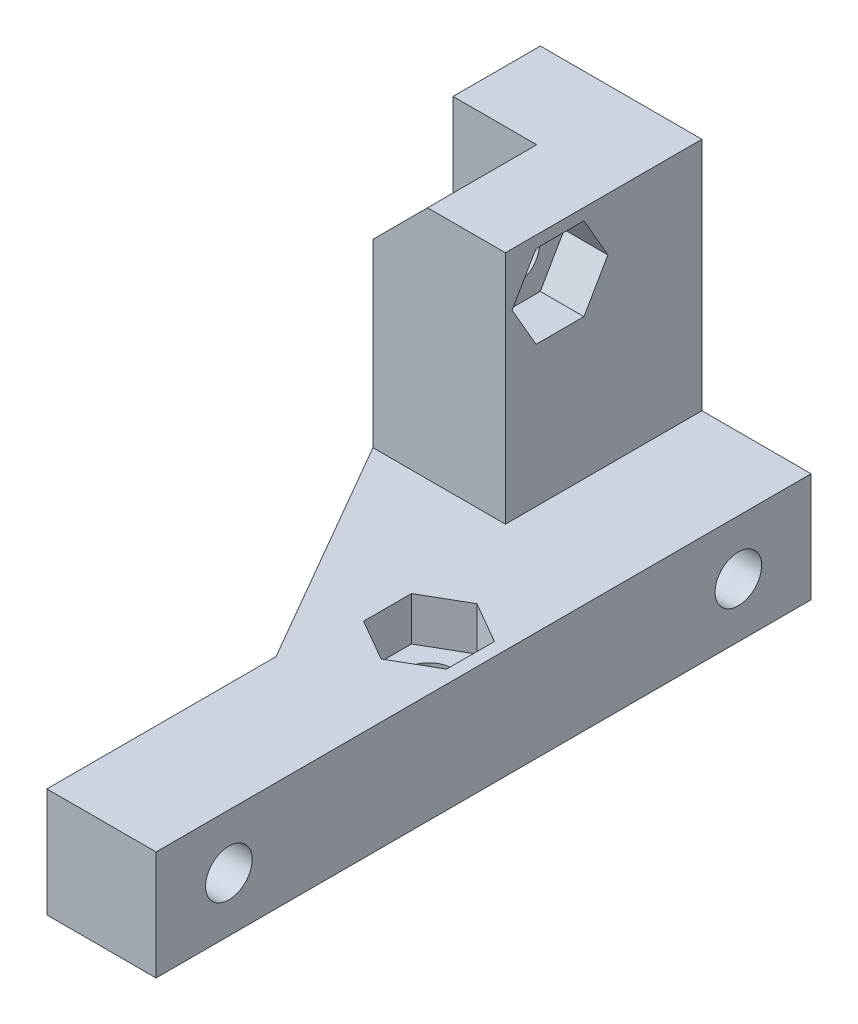
SolidWorks part; units mm, degrees
ref_plane "Alzado" through (0, 0, 0) normal (0, 0, 1) x (1, 0, 0)
ref_plane "Planta" through (0, 0, 0) normal (0, 1, 0) x (1, 0, 0)
ref_plane "Vista lateral" through (0, 0, 0) normal (1, 0, 0) x (0, 0, -1)
sketch "Croquis1" plane through (0, 0, 0) normal (0, 0, 1) x (1, 0, 0)
  line L0 (0, 0) -> (16.6, 0)
  line L1 (16.6, 0) -> (16.6, 7.5)
  line L2 (16.6, 7.5) -> (9.1, 7.5)
  line L3 (9.1, 7.5) -> (9.1, 23.65)
  line L4 (9.1, 23.65) -> (3.75, 23.65)
  line L5 (3.75, 23.65) -> (-2, 23.65)
  line L6 (0, 23.65) -> (0, 0) construction
  line L7 (0, 0) -> (-2, 0)
  line L8 (-2, 0) -> (-2, 23.65)
  line L10 (0, 0) -> (-2, 0)
  dimension "D1" = 7.5
  dimension "D3" = 3.75
  dimension "D4" = 16.6
  dimension "D5" = 7.5
  dimension "D6" = 23.65
  dimension "D7" = 2
extrude "Saliente-Extruir1" add sketch "Croquis1" along normal blind 6 contours L5 L6 L0 L1 L2 L3 L4 | L6 L5 L8 L7
sketch "Croquis2" plane through (0, 0, 6) normal (0, 0, 1) x (1, 0, 0)
  line L0 (0, 0) -> (0, 19.9)
  line L1 (0, 19.9) -> (3.75, 23.65)
  line L6 (9.1, 23.65) -> (-2, 23.65)
  line L7 (-2, 23.65) -> (-2, 0)
  line L8 (-2, 0) -> (16.6, 0)
  line L9 (16.6, 0) -> (16.6, 7.5)
  line L10 (16.6, 7.5) -> (9.1, 7.5)
  line L11 (9.1, 7.5) -> (9.1, 23.65)
  line L12 (9.1, 23.65) -> (3.75, 23.65)
  line L14 (0, 0) -> (16.6, 0)
  line L15 (16.6, 0) -> (16.6, 7.5)
  line L16 (16.6, 7.5) -> (9.1, 7.5)
  line L17 (9.1, 7.5) -> (9.1, 23.65)
  point P7 (0, 23.65)
  dimension "D4" = 3.75
  dimension "D1" = 0
extrude "Saliente-Extruir2" add sketch "Croquis2" along normal blind 7.5
sketch "Croquis3" plane through (0, 0, 0) normal (0, -1, 0) x (1, 0, 0)
  line L0 (0, 13.5) -> (9.1, 29.2617)
  line L1 (9.1, 29.2617) -> (9.1, 13.5)
  line L2 (0, 13.5) -> (16.6, 13.5) construction
  line L3 (0, 13.5) -> (9.1, 13.5)
  dimension "D1" = 7.5
  dimension "D2" = 60
extrude "Saliente-Extruir3" add sketch "Croquis3" against normal up to surface (7.5 mm away) up to face at (12.85, 7.5, 6.75)
ref_plane "Plano1" through (0, 0, 45) normal (0, 0, -1) x (-1, 0, 0)
sketch "Croquis4" plane through (0, 0, 13.5) normal (0, 0, 1) x (1, 0, 0)
  line L4 (16.6, 7.5) -> (9.1, 7.5)
  line L5 (9.1, 7.5) -> (9.1, 0)
  line L6 (9.1, 0) -> (16.6, 0)
  line L7 (16.6, 0) -> (16.6, 7.5)
  line L8 (16.6, 7.5) -> (9.1, 7.5)
  line L9 (9.1, 7.5) -> (9.1, 0)
  line L10 (9.1, 0) -> (16.6, 0)
  line L11 (16.6, 0) -> (16.6, 7.5)
  dimension "D1" = 0
extrude "Saliente-Extruir4" add sketch "Croquis4" along normal up to surface (31.5 mm away) up to plane "Plano1"
sketch "Croquis5" plane through (16.6, 0, 0) normal (1, 0, 0) x (0, 0, -1)
  line L0 (0, 3.75) -> (-5, 3.75) construction
  line L1 (0, 0) -> (0, 7.5) construction
  line L2 (-5, 3.75) -> (-40, 3.75) construction
  line L3 (-40, 3.75) -> (-45, 3.75) construction
  line L4 (-45, 7.5) -> (-45, 0) construction
  circle A0 centre (-5, 3.75) radius 1.6
  circle A1 centre (-40, 3.75) radius 1.6
  dimension "D2" = 3.2
  dimension "D1" = 35
extrude "Cortar-Extruir1" cut sketch "Croquis5" against normal up to next
sketch "Croquis6" plane through (-2, 0, 0) normal (-1, 0, 0) x (0, 0, 1)
  line L1 (3.3546, 0.9) -> (6.6454, 0.9)
  line L2 (6.6454, 0.9) -> (8.2909, 3.75)
  line L3 (8.2909, 3.75) -> (6.6454, 6.6)
  line L4 (6.6454, 6.6) -> (3.3546, 6.6)
  line L5 (3.3546, 6.6) -> (1.7091, 3.75)
  line L6 (1.7091, 3.75) -> (3.3546, 0.9)
  circle A0 centre (5, 3.75) radius 1.6 construction
  circle A1 centre (5, 3.75) radius 1.6 construction
  circle A2 centre (5, 3.75) radius 2.85 construction
  dimension "D1" = 5.7
extrude "Cortar-Extruir2" cut sketch "Croquis6" against normal offset from surface (14.1 mm away) 4.5 up to face at (16.6, 3.75, 38.4)
sketch "Croquis7" plane through (9.1, 0, 0) normal (-1, 0, 0) x (0, 0, 1)
  line L1 (38.3546, 0.9) -> (41.6454, 0.9)
  line L2 (41.6454, 0.9) -> (43.2909, 3.75)
  line L3 (43.2909, 3.75) -> (41.6454, 6.6)
  line L4 (41.6454, 6.6) -> (38.3546, 6.6)
  line L5 (38.3546, 6.6) -> (36.7091, 3.75)
  line L6 (36.7091, 3.75) -> (38.3546, 0.9)
  circle A0 centre (40, 3.75) radius 2.85 construction
  dimension "D1" = 5.7
extrude "Cortar-Extruir3" cut sketch "Croquis7" against normal blind 3
sketch "Croquis8" plane through (0, 0, 0) normal (0, -1, 0) x (1, 0, 0)
  line L0 (12.85, 45) -> (12.85, 0) construction
  line L1 (16.6, 45) -> (9.1, 45) construction
  line L2 (-2, 0) -> (16.6, 0) construction
  circle A0 centre (12.85, 22.5) radius 1.6
  dimension "D1" = 3.2
extrude "Cortar-Extruir4" cut sketch "Croquis8" against normal up to next
sketch "Croquis9" plane through (0, 7.5, 0) normal (0, 1, 0) x (1, 0, 0)
  line L1 (15.7, -20.8546) -> (12.85, -19.2091)
  line L2 (12.85, -19.2091) -> (10, -20.8546)
  line L3 (10, -20.8546) -> (10, -24.1454)
  line L4 (10, -24.1454) -> (12.85, -25.7909)
  line L5 (12.85, -25.7909) -> (15.7, -24.1454)
  line L6 (15.7, -24.1454) -> (15.7, -20.8546)
  circle A0 centre (12.85, -22.5) radius 2.85 construction
  dimension "D1" = 5.7
extrude "Cortar-Extruir5" cut sketch "Croquis9" against normal blind 3
sketch "Croquis10" plane through (9.1, 0, 0) normal (1, 0, 0) x (0, 0, -1)
  line L0 (-13.5, 23.65) -> (-6, 23.65) construction
  line L1 (-13.5, 23.65) -> (-6, 23.65) construction
  line L2 (-9.75, 23.65) -> (-9.75, 20) construction
  circle A0 centre (-9.75, 20) radius 1.6
  dimension "D1" = 3.2
  dimension "D2" = 3.65
extrude "Cortar-Extruir6" cut sketch "Croquis10" against normal up to next
sketch "Croquis11" plane through (9.1, 0, 0) normal (1, 0, 0) x (0, 0, -1)
  line L1 (-8.1046, 22.85) -> (-11.3954, 22.85)
  line L2 (-11.3954, 22.85) -> (-13.0409, 20)
  line L3 (-13.0409, 20) -> (-11.3954, 17.15)
  line L4 (-11.3954, 17.15) -> (-8.1046, 17.15)
  line L5 (-8.1046, 17.15) -> (-6.4591, 20)
  line L6 (-6.4591, 20) -> (-8.1046, 22.85)
  circle A0 centre (-9.75, 20) radius 2.85 construction
  dimension "D1" = 5.7
extrude "Cortar-Extruir7" cut sketch "Croquis11" against normal blind 3
